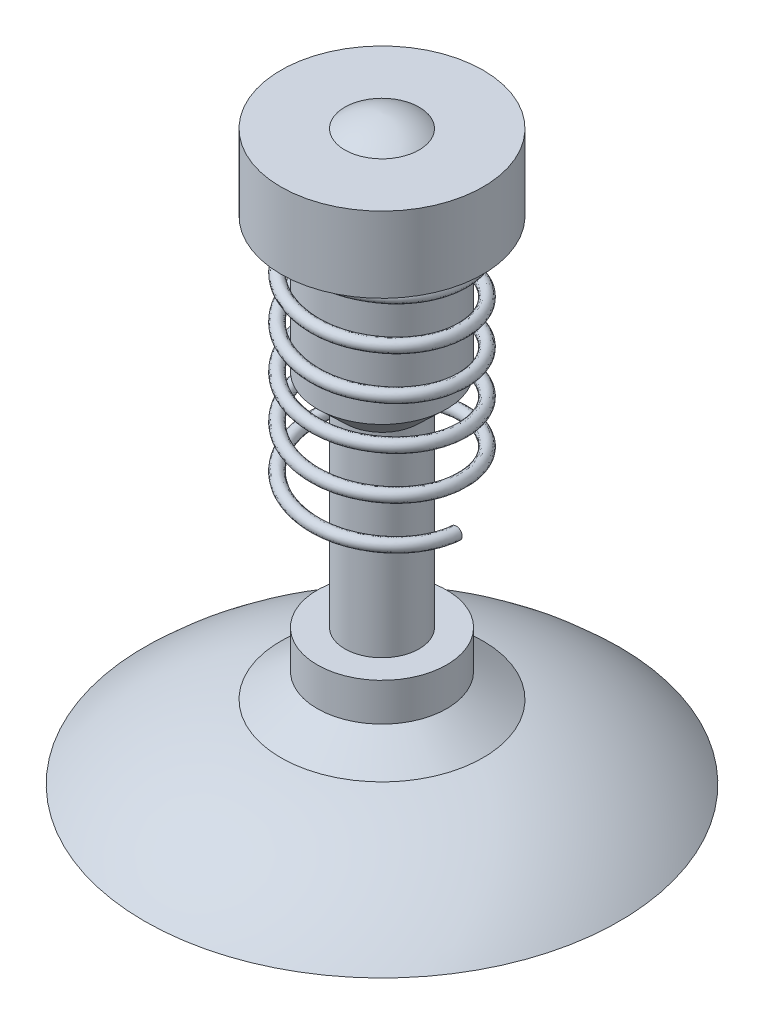
SolidWorks part; units mm, degrees
ref_plane "Front Plane" through (0, 0, 0) normal (0, 0, 1) x (1, 0, 0)
ref_plane "Top Plane" through (0, 0, 0) normal (0, 1, 0) x (1, 0, 0)
ref_plane "Right Plane" through (0, 0, 0) normal (1, 0, 0) x (0, 0, -1)
sketch "Sketch1" plane through (0, 0, 0) normal (0, 0, 1) x (1, 0, 0)
  line L0 (0, 2.69) -> (0, 0)
  line L1 (0, 0) -> (1.1, 0)
  line L2 (0.4685, 0.34) -> (0.3, 0.4527)
  line L3 (0.3, 0.4527) -> (0.3, 0.6285)
  line L4 (0.3, 0.6285) -> (0.172, 0.6285)
  line L5 (0.172, 0.6285) -> (0.172, 1.5329)
  line L6 (0.172, 1.5329) -> (0.3, 1.655)
  line L7 (0.3, 1.655) -> (0.3, 2.28)
  line L8 (0.3, 2.28) -> (0.4685, 2.28)
  line L9 (0.4685, 2.28) -> (0.4685, 2.63)
  line L10 (0.4685, 2.63) -> (0.172, 2.63)
  arc A0 (1.1, 0) -> (0.4685, 0.34) centre (0.1779, -0.956) ccw
  arc A1 (0.172, 2.63) -> (0, 2.69) centre (-0.015, 2.3706) ccw
  point P16 (0.5102, 0.2024)
  point P17 (0.3143, 0.4221)
  point P18 (0.2964, 1.4551)
  point P19 (0.172, 2.63)
  point P20 (0.172, 1.2558)
  point P21 (0.172, 1.5329)
  point P22 (0.3, 0.4527)
  point P23 (0.4685, 0.34)
  dimension "D1" = 2.69
  dimension "D2" = 1.1
  dimension "D3" = 0.35
  dimension "D4" = 0.625
  dimension "D5" = 0.172
  dimension "D6" = 0.3
  dimension "D7" = 0.3
  dimension "D8" = 0.06
revolve "Revolve1" add sketch "Sketch1" angle 360 about L0
sketch "Sketch2" plane through (0, 2.28, 0) normal (0, -1, 0) x (1, 0, 0)
  circle A0 centre (0, 0) radius 0.344
  dimension "D1" = 0.688
curve "Helix/Spiral1" pitch 0.2 height 1.1 turns 5.5
sketch "Sketch3" plane through (0, 0, 0) normal (0, 0, 1) x (1, 0, 0)
  circle A0 centre (0.344, 2.18) radius 0.0275
  dimension "D1" = 0.055
sweep "Sweep1" add profiles "Sketch3" path "Helix/Spiral1"
